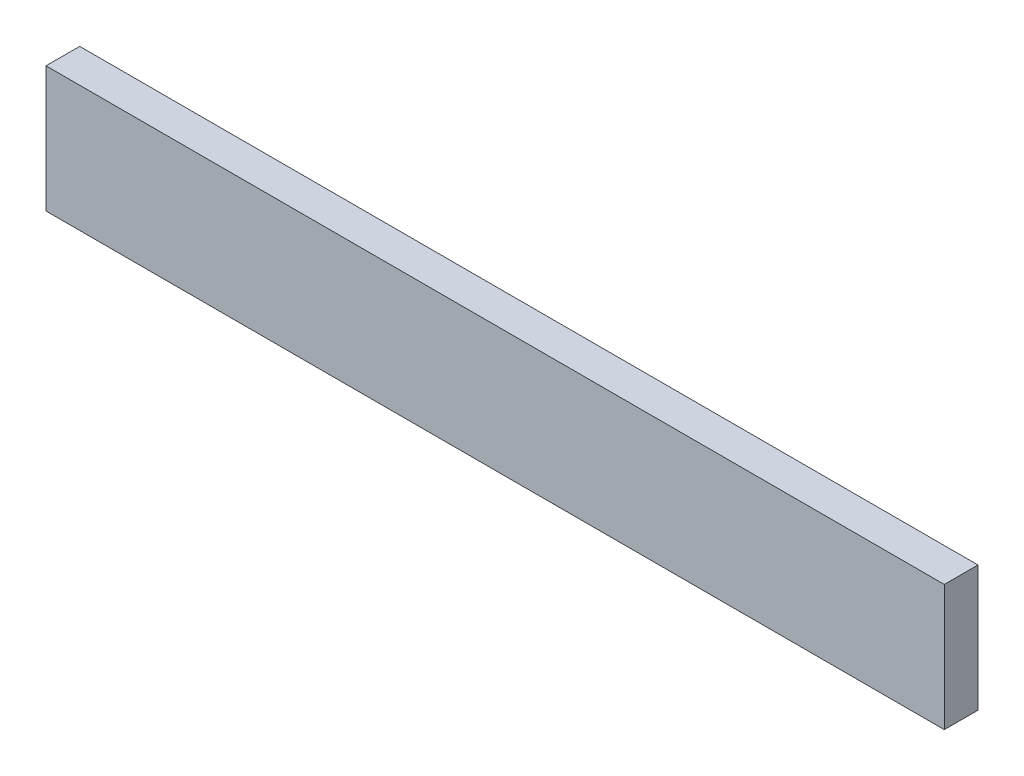
SolidWorks part; units mm, degrees
ref_plane "Front Plane" through (0, 0, 0) normal (0, 0, 1) x (1, 0, 0)
ref_plane "Top Plane" through (0, 0, 0) normal (0, 1, 0) x (1, 0, 0)
ref_plane "Right Plane" through (0, 0, 0) normal (1, 0, 0) x (0, 0, -1)
sketch "Sketch1" plane through (0, 0, 0) normal (0, 0, 1) x (1, 0, 0)
  line L1 (0, 0) -> (80, 0)
  line L2 (0, 0) -> (0, 11.2)
  line L3 (0, 11.2) -> (80, 11.2)
  line L4 (80, 0) -> (80, 11.2)
sketch "Sketch2" plane through (0, 0, 0) normal (1, 0, 0) x (0, 0, -1)
  line L1 (-3, 11.2) -> (0, 11.2)
  line L2 (-3, 11.2) -> (-3, 0)
  line L3 (-3, 0) -> (0, 0)
  line L4 (0, 11.2) -> (0, 0)
extrude "Boss-Extrude1" add sketch "Sketch1" along normal up to vertex (3 mm away) up to point (0, 0, 3)
